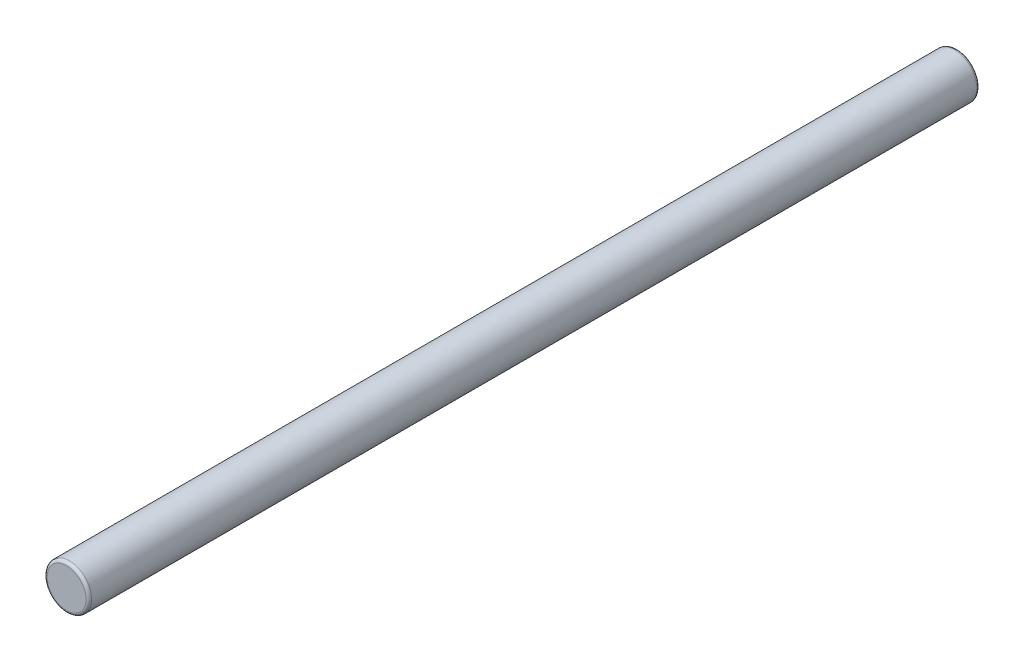
SolidWorks part; units mm, degrees
ref_plane "Front Plane" through (0, 0, 0) normal (0, 0, 1) x (1, 0, 0)
ref_plane "Top Plane" through (0, 0, 0) normal (0, 1, 0) x (1, 0, 0)
ref_plane "Right Plane" through (0, 0, 0) normal (1, 0, 0) x (0, 0, -1)
sketch "Sketch1" plane through (0, 0, 0) normal (0, 0, 1) x (1, 0, 0)
  circle A0 centre (0, 0) radius 1
  dimension "D1" = 2
extrude "Boss-Extrude1" add sketch "Sketch1" along normal mid plane 40
fillet "Fillet1" radius 0.127 2 edges at (1, 0, -20) (1, 0, 20)
